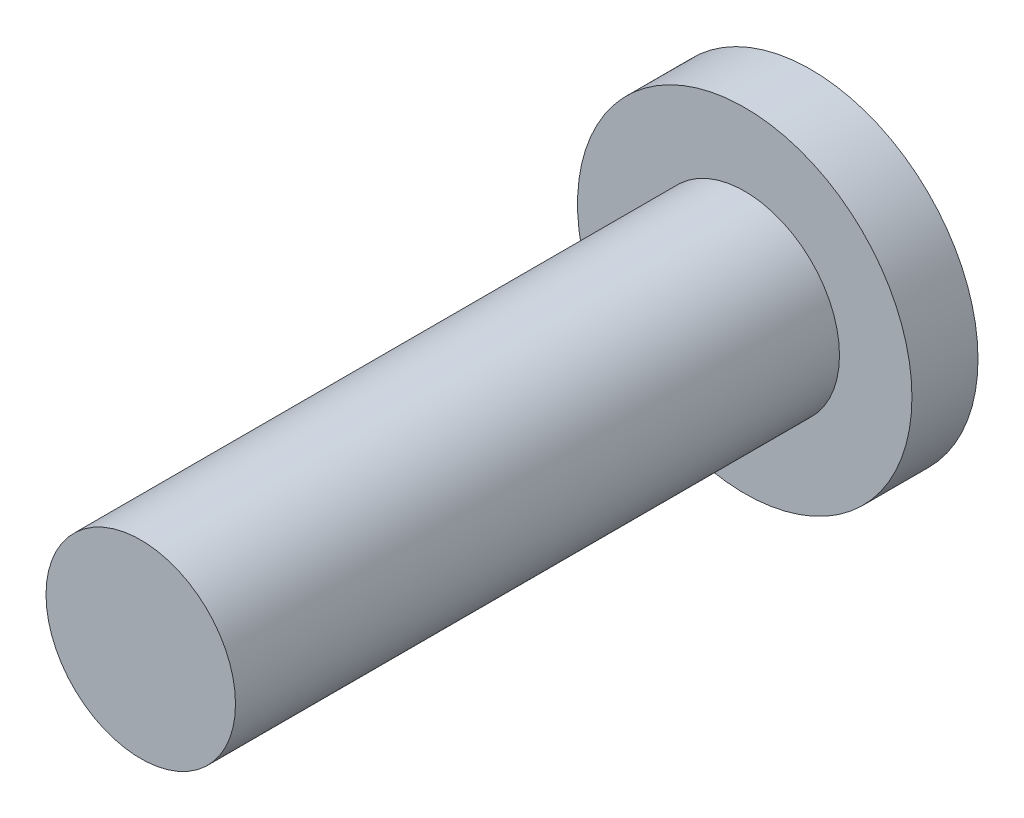
SolidWorks part; units mm, degrees
ref_plane "Front Plane" through (0, 0, 0) normal (0, 0, 1) x (1, 0, 0)
ref_plane "Top Plane" through (0, 0, 0) normal (0, 1, 0) x (1, 0, 0)
ref_plane "Right Plane" through (0, 0, 0) normal (1, 0, 0) x (0, 0, -1)
sketch "Sketch1" plane through (0, 0, 0) normal (0, 0, 1) x (1, 0, 0)
  circle A0 centre (-10.0603, 7.7464) radius 4.5
extrude "Boss-Extrude2" add sketch "Sketch1" along normal blind 1.778
sketch "Sketch2" plane through (0, 0, 1.778) normal (0, 0, 1) x (1, 0, 0)
  line L0 (-10.8947, 12.1684) -> (-10.0603, 7.7464) construction
  line L1 (-10.0603, 7.7464) -> (-9.2259, 3.3244) construction
  circle A0 centre (-10.0603, 7.7464) radius 4.5 construction
  circle A1 centre (-10.0603, 7.7464) radius 2.55
extrude "Boss-Extrude4" add sketch "Sketch2" along normal blind 16.256
